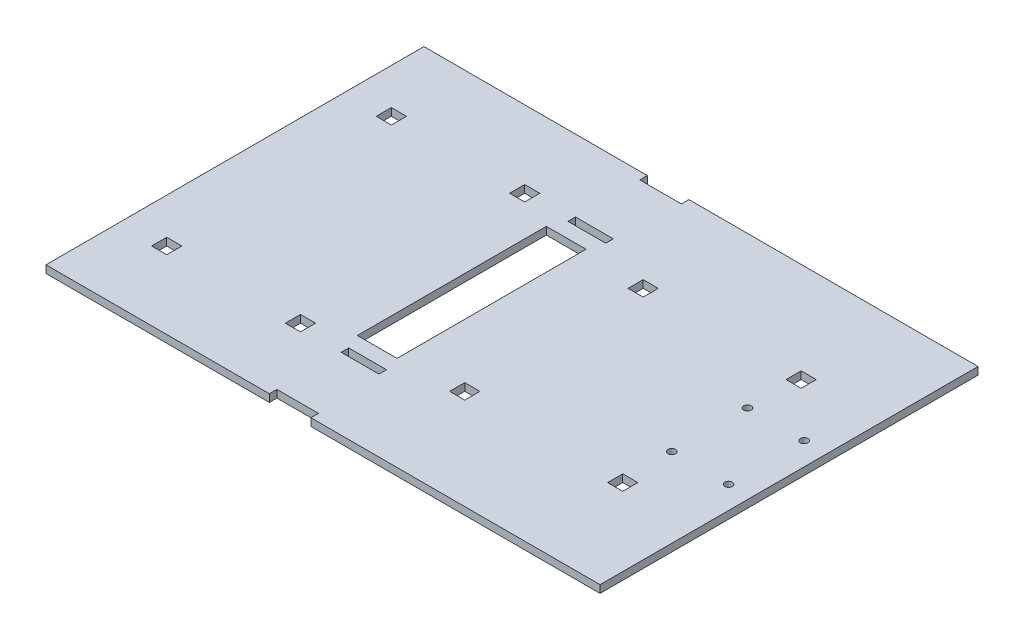
SolidWorks part; units mm, degrees
ref_plane "Front Plane" through (0, 0, 0) normal (0, 0, 1) x (1, 0, 0)
ref_plane "Top Plane" through (0, 0, 0) normal (0, 1, 0) x (1, 0, 0)
ref_plane "Right Plane" through (0, 0, 0) normal (1, 0, 0) x (0, 0, -1)
sketch "Sketch1" plane through (0, 0, 0) normal (0, 1, 0) x (1, 0, 0)
  line L0 (-18.034, 63.5) -> (-18.034, 60.96)
  line L1 (-93.091, -63.5) -> (-18.034, -63.5)
  line L2 (-93.091, -63.5) -> (-93.091, 63.5)
  line L3 (-93.091, 63.5) -> (-18.034, 63.5)
  line L4 (93.091, -63.5) -> (93.091, 63.5)
  line L5 (-18.034, 60.96) -> (-4.064, 60.96)
  line L6 (-4.064, 60.96) -> (-4.064, 63.5)
  line L7 (-93.091, 0) -> (93.091, 0) construction
  line L8 (-4.064, 63.5) -> (93.091, 63.5)
  line L9 (-4.064, -60.96) -> (-4.064, -63.5)
  line L10 (-18.034, -60.96) -> (-4.064, -60.96)
  line L11 (-18.034, -63.5) -> (-18.034, -60.96)
  line L12 (-4.064, -63.5) -> (93.091, -63.5)
  point P0 (0, 0)
  point P7 (-93.091, 0)
  point P15 (0, 0)
  dimension "D1" = 127
  dimension "D2" = 97.155
  dimension "D3" = 75.057
  dimension "D4" = 13.97
  dimension "D5" = 2.54
extrude "Boss-Extrude1" add sketch "Sketch1" against normal blind 2.54
sketch "Sketch2" plane through (0, 0, 0) normal (0, 1, 0) x (1, 0, 0)
  line L0 (-93.091, -63.5) -> (-18.034, -63.5) construction
  line L1 (-80.8228, -35.2044) -> (-75.7428, -35.2044)
  line L2 (-80.8228, -35.2044) -> (-80.8228, -40.2844)
  line L3 (-80.8228, -40.2844) -> (-75.7428, -40.2844)
  line L4 (-75.7428, -35.2044) -> (-75.7428, -40.2844)
  line L5 (-93.091, 63.5) -> (-93.091, -63.5) construction
  line L6 (-80.8228, 40.2844) -> (-75.7428, 40.2844)
  line L7 (-75.7428, 35.2044) -> (-75.7428, 40.2844)
  line L12 (-80.8228, 35.2044) -> (-75.7428, 35.2044)
  line L22 (93.091, 63.5) -> (-4.064, 63.5) construction
  line L23 (-20.2184, 31.75) -> (-6.8834, 31.75)
  line L24 (-20.2184, 31.75) -> (-20.2184, -31.75)
  line L25 (-20.2184, -31.75) -> (-6.8834, -31.75)
  line L26 (-6.8834, 31.75) -> (-6.8834, -31.75)
  line L27 (93.091, 0) -> (-93.091, 0) construction
  line L28 (-18.034, 39.37) -> (-5.334, 39.37)
  line L29 (-18.034, -36.83) -> (-5.334, -36.83)
  line L30 (-18.034, -36.83) -> (-18.034, -39.37)
  line L31 (-18.034, -39.37) -> (-5.334, -39.37)
  line L32 (-5.334, -36.83) -> (-5.334, -39.37)
  line L33 (-5.334, 36.83) -> (-5.334, 39.37)
  line L34 (-18.034, 36.83) -> (-5.334, 36.83)
  line L35 (-18.034, 36.83) -> (-18.034, 39.37)
  line L36 (93.091, -63.5) -> (93.091, 63.5) construction
  line L37 (-4.064, -63.5) -> (93.091, -63.5) construction
  line L38 (85.471, -12.7) -> (66.421, -12.7) construction
  line L40 (64.643, -27.432) -> (69.723, -27.432)
  line L41 (64.643, -27.432) -> (64.643, -32.512)
  line L42 (64.643, -32.512) -> (69.723, -32.512)
  line L43 (69.723, -27.432) -> (69.723, -32.512)
  line L55 (-80.8228, 35.2044) -> (-80.8228, 40.2844)
  line L56 (-30.9372, 35.2044) -> (-30.9372, 40.2844)
  line L57 (-30.9372, 35.2044) -> (-36.0172, 35.2044)
  line L58 (-36.0172, 35.2044) -> (-36.0172, 40.2844)
  line L59 (-30.9372, 40.2844) -> (-36.0172, 40.2844)
  line L60 (-30.8102, -40.2844) -> (-35.8902, -40.2844)
  line L61 (-35.8902, -35.2044) -> (-35.8902, -40.2844)
  line L62 (-30.8102, -35.2044) -> (-35.8902, -35.2044)
  line L63 (-30.8102, -35.2044) -> (-30.8102, -40.2844)
  line L64 (64.643, 32.512) -> (69.723, 32.512)
  line L65 (69.723, 27.432) -> (69.723, 32.512)
  line L66 (64.643, 27.432) -> (69.723, 27.432)
  line L67 (64.643, 27.432) -> (64.643, 32.512)
  line L68 (64.643, 32.512) -> (16.637, 32.512) construction
  line L69 (16.637, 27.432) -> (16.637, 32.512)
  line L70 (11.557, 27.432) -> (11.557, 32.512)
  line L71 (11.557, 27.432) -> (16.637, 27.432)
  line L72 (11.557, 32.512) -> (16.637, 32.512)
  line L73 (11.557, -27.432) -> (16.637, -27.432)
  line L74 (11.557, -27.432) -> (11.557, -32.512)
  line L75 (11.557, -32.512) -> (16.637, -32.512)
  line L76 (16.637, -27.432) -> (16.637, -32.512)
  circle A0 centre (85.471, -12.7) radius 1.27
  circle A1 centre (66.421, -12.7) radius 1.27
  circle A2 centre (85.471, 12.7) radius 1.27
  circle A3 centre (66.421, 12.7) radius 1.27
  point P35 (0, 0)
  dimension "D14" = 2.54
  dimension "D16" = 25.4
  dimension "D1" = 5.08
  dimension "D2" = 23.2156
  dimension "D3" = 12.2682
  dimension "D4" = 10.7188
  dimension "D5" = 48.006
  dimension "D6" = 63.5
  dimension "D7" = 13.335
  dimension "D8" = 31.75
  dimension "D9" = 39.8526
  dimension "D10" = 12.7
  dimension "D11" = 2.54
  dimension "D12" = 1.27
  dimension "D13" = 5.08
  dimension "D15" = 7.62
  dimension "D17" = 19.05
  dimension "D18" = 23.368
  dimension "D19" = 30.988
extrude "Cut-Extrude1" cut sketch "Sketch2" against normal up to next
